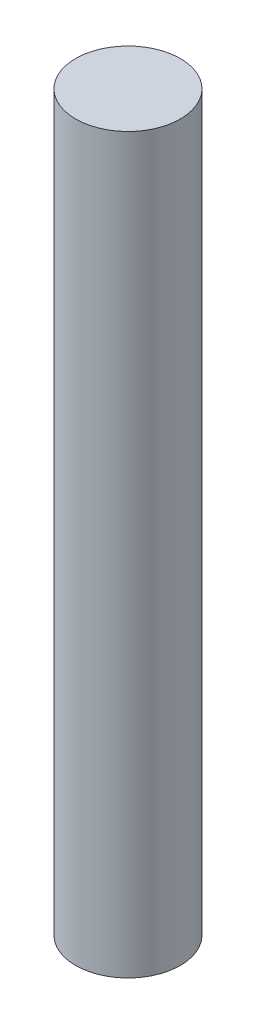
SolidWorks part; units mm, degrees
ref_plane "Front Plane" through (0, 0, 0) normal (0, 0, 1) x (1, 0, 0)
ref_plane "Top Plane" through (0, 0, 0) normal (0, 1, 0) x (1, 0, 0)
ref_plane "Right Plane" through (0, 0, 0) normal (1, 0, 0) x (0, 0, -1)
sketch "Sketch1" plane through (0, 0, 0) normal (0, 1, 0) x (1, 0, 0)
  circle A0 centre (0, 0) radius 5
  dimension "D1" = 10
extrude "Boss-Extrude1" add sketch "Sketch1" along normal blind 70
